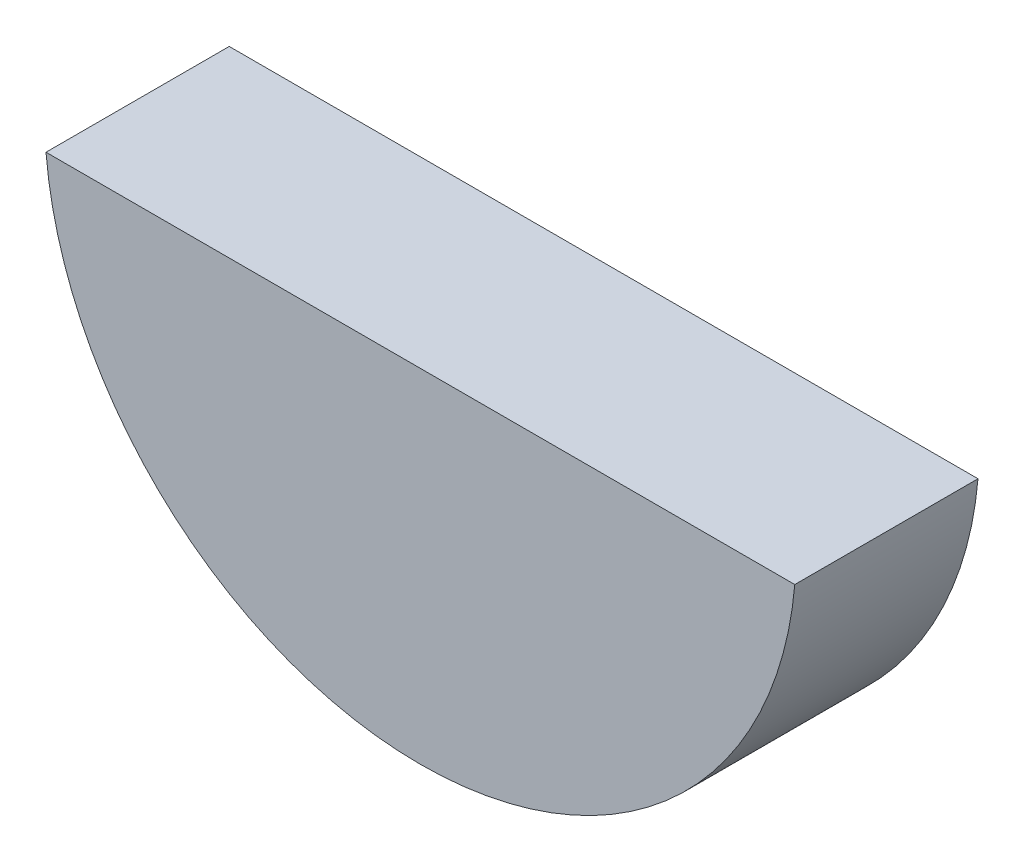
SolidWorks part; units mm, degrees
ref_plane "Piano frontale" through (0, 0, 0) normal (0, 0, 1) x (1, 0, 0)
ref_plane "Piano superiore" through (0, 0, 0) normal (0, 1, 0) x (1, 0, 0)
ref_plane "Piano destro" through (0, 0, 0) normal (1, 0, 0) x (0, 0, -1)
sketch "Schizzo1" plane through (0, 0, 0) normal (0, 0, 1) x (1, 0, 0)
  line L0 (-8, 0) -> (8, 0)
  arc A0 (-8, 0) -> (8, 0) centre (0, 0) ccw
  dimension "D1" = 16
extrude "Estrusione-Estrusione1" add sketch "Schizzo1" along normal blind 3.9
sketch "Schizzo2" plane through (0, 0, 0) normal (0, 1, 0) x (1, 0, 0)
  line L4 (8, 0) -> (-8, 0)
  line L5 (-8, 0) -> (-8, -3.9)
  line L6 (-8, -3.9) -> (8, -3.9)
  line L7 (8, -3.9) -> (8, 0)
  line L8 (8, 0) -> (-8, 0)
  line L9 (-8, 0) -> (-8, -3.9)
  line L10 (-8, -3.9) -> (8, -3.9)
  line L11 (8, -3.9) -> (8, 0)
  dimension "D1" = 0
extrude "Taglio-Estrusione1" cut sketch "Schizzo2" against normal blind 0.7
